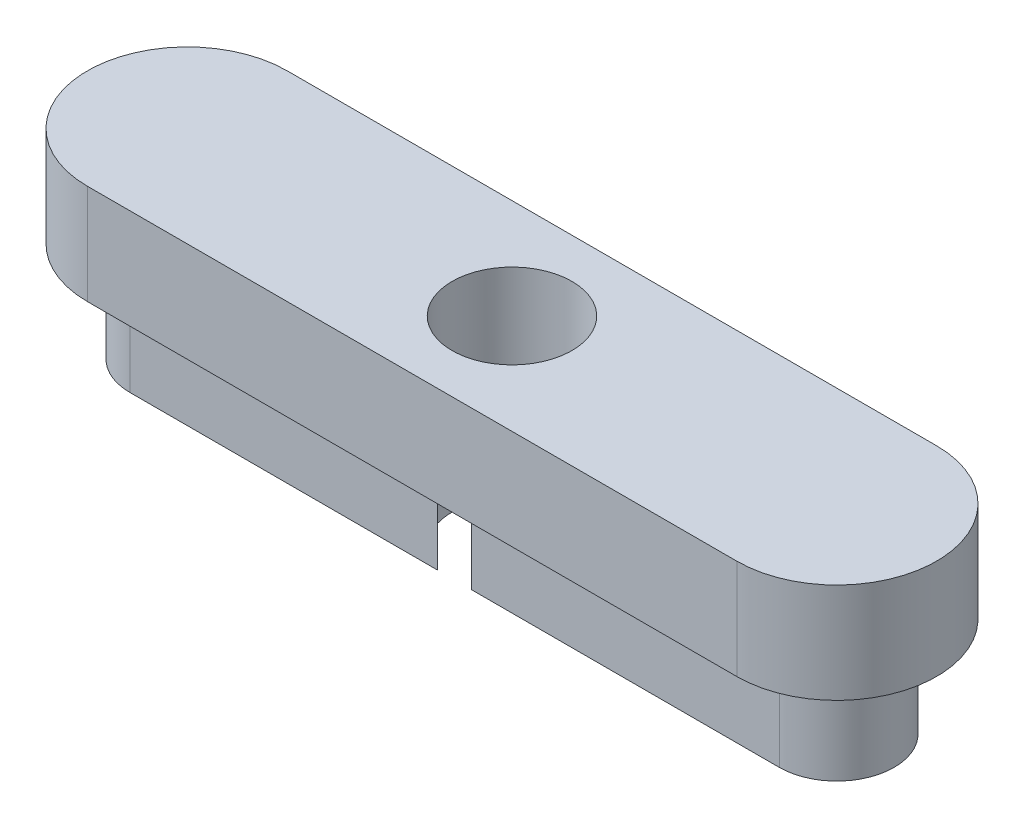
SolidWorks part; units mm, degrees
ref_plane "Front Plane" through (0, 0, 0) normal (0, 0, 1) x (1, 0, 0)
ref_plane "Top Plane" through (0, 0, 0) normal (0, 1, 0) x (1, 0, 0)
ref_plane "Right Plane" through (0, 0, 0) normal (1, 0, 0) x (0, 0, -1)
sketch "Sketch1" plane through (0, 0, 0) normal (0, 1, 0) x (1, 0, 0)
  line L0 (-6.5, 0) -> (6.5, 0) construction
  line L1 (-6.5, 2) -> (6.5, 2)
  line L2 (-6.5, -2) -> (6.5, -2)
  arc A0 (-6.5, 2) -> (-6.5, -2) centre (-6.5, 0) ccw
  arc A1 (6.5, -2) -> (6.5, 2) centre (6.5, 0) ccw
  point P2 (0, 0)
  dimension "D1" = 13
  dimension "D2" = 4
extrude "Boss-Extrude1" add sketch "Sketch1" along normal blind 2
sketch "Sketch2" plane through (0, 0, 0) normal (0, -1, 0) x (1, 0, 0)
  line L0 (-6.5, 0) -> (6.5, 0) construction
  line L1 (-6.5, 1.15) -> (6.5, 1.15)
  line L2 (-6.5, -1.15) -> (6.5, -1.15)
  line L3 (6.5, 1.2) -> (-6.5, 1.2) construction
  arc A0 (-6.5, 1.15) -> (-6.5, -1.15) centre (-6.5, 0) ccw
  arc A1 (6.5, -1.15) -> (6.5, 1.15) centre (6.5, 0) ccw
  point P2 (0, 0)
  point P10 (6.2, 0)
  dimension "D2" = 13
  dimension "D1" = 0.05
extrude "Boss-Extrude2" add sketch "Sketch2" along normal blind 2
sketch "Sketch3" plane through (0, -2, 0) normal (0, -1, 0) x (1, 0, 0)
  circle A0 centre (0, 0) radius 1.2
  dimension "D1" = 2.4
extrude "Cut-Extrude1" cut sketch "Sketch3" against normal through all
